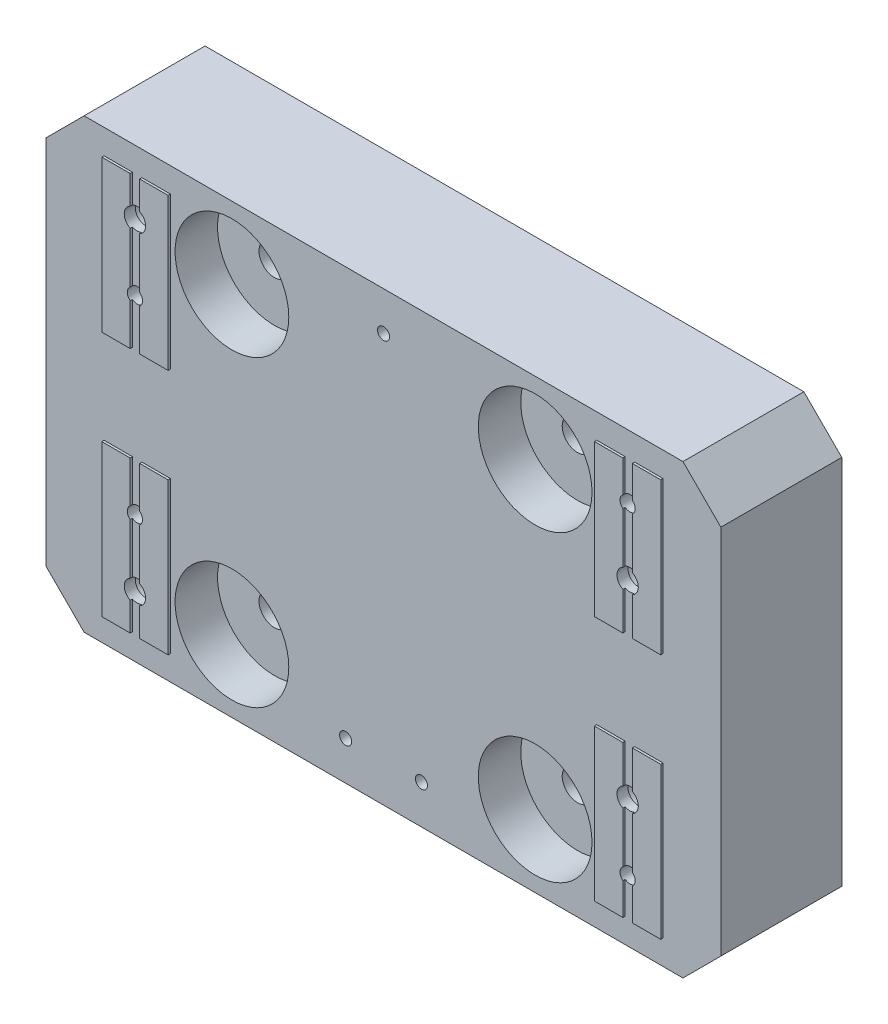
SolidWorks part; units mm, degrees
material "304 SSTL"
ref_plane "Front" through (0, 0, 0) normal (0, 0, 1) x (1, 0, 0)
ref_plane "Top" through (0, 0, 0) normal (0, 1, 0) x (1, 0, 0)
ref_plane "Right" through (0, 0, 0) normal (1, 0, 0) x (0, 0, -1)
sketch "Sketch3" plane through (0, 0, 0) normal (0, 0, 1) x (1, 0, 0)
  line L1 (0, 0) -> (226.06, 0)
  line L2 (0, 0) -> (0, -149.86)
  line L3 (0, -149.86) -> (226.06, -149.86)
  line L4 (226.06, 0) -> (226.06, -149.86)
  dimension "D1" = 226.06
  dimension "D2" = 149.86
extrude "Extrude2" add sketch "Sketch3" along normal blind 41.275
sketch "Sketch4" plane through (0, 0, 41.275) normal (0, 0, 1) x (1, 0, 0)
  line L0 (113.03, 0) -> (113.03, -149.86) construction
  line L1 (0, -74.93) -> (226.06, -74.93) construction
  line L2 (19.3802, -59.055) -> (19.3802, -8.255)
  line L3 (19.3802, -8.255) -> (41.6052, -8.255)
  line L4 (206.6798, -59.055) -> (206.6798, -8.255)
  line L5 (184.4548, -8.255) -> (206.6798, -8.255)
  line L6 (19.3802, -90.805) -> (19.3802, -141.605)
  line L7 (41.6052, -8.255) -> (41.6052, -59.055)
  line L8 (19.3802, -141.605) -> (41.6052, -141.605)
  line L9 (184.4548, -141.605) -> (206.6798, -141.605)
  line L10 (41.6052, -141.605) -> (41.6052, -90.805)
  line L11 (206.6798, -90.805) -> (206.6798, -141.605)
  line L13 (184.4548, -141.605) -> (184.4548, -90.805)
  line L16 (184.4548, -8.255) -> (184.4548, -59.055)
  line L19 (0, 0) -> (226.06, 0)
  line L20 (0, 0) -> (0, -149.86)
  line L21 (0, -149.86) -> (226.06, -149.86)
  line L22 (226.06, 0) -> (226.06, -149.86)
  line L23 (19.3802, -59.055) -> (41.6052, -59.055)
  line L24 (19.3802, -90.805) -> (41.6052, -90.805)
  line L27 (184.4548, -59.055) -> (206.6798, -59.055)
  line L28 (184.4548, -90.805) -> (206.6798, -90.805)
  dimension "D1" = 71.4248
  dimension "D2" = 71.4248
  dimension "D3" = 22.225
  dimension "D5" = 15.875
  dimension "D6" = 15.875
  dimension "D8" = 50.8
extrude "Extrude4" cut sketch "Sketch4" against normal blind 0.762
hole_wizard "CBORE for 1/4 Socket Head Cap Screw1" positions "3DSketch4" profile "Sketch9" counterbore size "1/4" standard "Ansi Inch" end condition through all
sketch3d "3DSketch4"
  line L1 (226.06, -74.93, 0) -> (0, -74.93, 0) construction
  line L2 (226.06, -149.86, 0) -> (226.06, 0, 0) construction
  line L3 (0, 0, 0) -> (0, -149.86, 0) construction
  line L5 (113.03, 0, 0) -> (113.03, -149.86, 0) construction
  line L6 (226.06, 0, 0) -> (0, 0, 0) construction
  line L7 (0, -149.86, 0) -> (226.06, -149.86, 0) construction
  line L10 (195.58, -43.18, 0) -> (195.58, -74.93, 0) construction
  line L12 (195.58, -74.93, 0) -> (195.58, -106.68, 0) construction
  line L14 (30.48, -20.955, 0) -> (30.48, -74.93, 0) construction
  line L16 (30.48, -74.93, 0) -> (30.48, -128.905, 0) construction
  point P4 (195.58, -106.68, 0)
  point P6 (30.48, -20.955, 0)
  point P8 (30.48, -128.905, 0)
  point P10 (195.58, -43.18, 0)
  dimension "D1" = 82.55
  dimension "D2" = 63.5
  dimension "D3" = 107.95
  dimension "D4" = 82.55
sketch "Sketch9" plane through (195.58, -106.68, 0) normal (1, 0, 0) x (0, 1, 0)
  line L0 (0, 0) -> (0, 41.275)
  line L1 (0, 41.275) -> (3.5712, 41.275)
  line L3 (3.5712, 41.275) -> (3.5712, 37.592)
  line L4 (5.5562, 37.592) -> (3.5712, 37.592)
  line L5 (5.5562, 37.592) -> (5.5562, 0.635)
  line L6 (5.5562, 0.635) -> (6.1913, 0)
  line L7 (6.1913, 0) -> (0, 0)
  line L8 (-5.5562, 0.635) -> (-6.1913, 0) construction
  line L11 (0, -6.35) -> (0, 107.95) construction
  dimension "Thru Hole Dia." = 7.1425
  dimension "Thru Hole Depth" = 41.275
  dimension "C'Bore Dia." = 11.1125
  dimension "C'Bore Depth" = 37.592
  dimension "Near C'Sink Dia." = 12.3825
  dimension "Near C'Sink Angle" = 90
hole_wizard "1/4-20 Tapped Hole1" positions "Sketch13" profile "Sketch12" tap size "1/4-20" standard "Ansi Inch" end condition through all
sketch "Sketch13" plane through (0, 0, 0) normal (0, 0, -1) x (-1, 0, 0)
  line L0 (-226.06, -74.93) -> (0, -74.93) construction
  line L1 (-226.06, -149.86) -> (-226.06, 0) construction
  line L2 (0, 0) -> (0, -149.86) construction
  line L4 (-113.03, 0) -> (-113.03, -149.86) construction
  line L5 (-226.06, 0) -> (0, 0) construction
  line L6 (0, -149.86) -> (-226.06, -149.86) construction
  line L11 (-195.58, -20.955) -> (-195.58, -74.93) construction
  line L13 (-195.58, -74.93) -> (-195.58, -128.905) construction
  line L15 (-30.48, -43.18) -> (-30.48, -74.93) construction
  line L17 (-30.48, -74.93) -> (-30.48, -106.68) construction
  point P3 (-195.58, -20.955)
  point P5 (-195.58, -128.905)
  point P7 (-30.48, -43.18)
  point P9 (-30.48, -106.68)
  dimension "D1" = 82.55
  dimension "D2" = 82.55
  dimension "D3" = 107.95
  dimension "D4" = 63.5
cosmetic thread "Hole Thread5" parameters "D1"=19.05, "D2"=6.35
cosmetic thread "Hole Thread6" parameters "D1"=19.05, "D2"=6.35
cosmetic thread "Hole Thread7" parameters "D1"=19.05, "D2"=6.35
cosmetic thread "Hole Thread8" parameters "D1"=19.05, "D2"=6.35
sketch "Sketch12" plane through (195.58, -20.955, 0) normal (1, 0, 0) x (0, 1, 0)
  line L0 (0, 0) -> (0, 41.275)
  line L1 (0, 41.275) -> (2.5527, 41.275)
  line L2 (2.5527, 41.275) -> (2.5527, 0)
  line L5 (2.5527, 0) -> (0, 0)
  line L11 (0, -6.35) -> (0, 107.95) construction
  dimension "Thru Tap Drill Dia." = 5.1054
  dimension "Thru Tap Drill Depth" = 41.275
hole_wizard "CBORE for 3/8 Socket Head Cap Screw1" positions "Sketch17" profile "Sketch16" counterbore size "3/8" standard "Ansi Inch" end condition through all
sketch "Sketch17" plane through (0, 0, 40.513) normal (0, 0, 1) x (1, 0, 0)
  line L0 (163.83, -125.73) -> (62.23, -125.73) construction
  line L1 (163.83, -125.73) -> (163.83, -24.13) construction
  line L2 (163.83, -24.13) -> (62.23, -24.13) construction
  line L3 (62.23, -125.73) -> (62.23, -24.13) construction
  line L4 (113.03, -149.86) -> (113.03, -125.73) construction
  line L5 (0, -149.86) -> (226.06, -149.86) construction
  line L6 (226.06, -74.93) -> (163.83, -74.93) construction
  line L7 (226.06, -149.86) -> (226.06, 0) construction
  point P0 (163.83, -125.73)
  point P1 (62.23, -125.73)
  point P3 (163.83, -24.13)
  point P5 (62.23, -24.13)
  dimension "D1" = 101.6
  dimension "D2" = 101.6
sketch "Sketch16" plane through (163.83, -125.73, 40.513) normal (1, 0, 0) x (0, -1, 0)
  line L0 (0, 0) -> (0, 40.513)
  line L1 (0, 40.513) -> (5.1587, 40.513)
  line L3 (5.1587, 40.513) -> (5.1587, 14.224)
  line L4 (5.1587, 14.224) -> (19.05, 14.224)
  line L5 (19.05, 14.224) -> (19.05, 0)
  line L7 (19.05, 0) -> (0, 0)
  line L11 (0, -6.35) -> (0, 107.95) construction
  dimension "Thru Hole Dia." = 10.3175
  dimension "Thru Hole Depth" = 40.513
  dimension "C'Bore Dia." = 38.1
  dimension "C'Bore Depth" = 14.224
sketch "Sketch18" plane through (0, 0, 41.275) normal (0, 0, 1) x (1, 0, 0)
  line L0 (30.48, -20.955) -> (30.48, -8.255) construction
  line L1 (28.8925, -8.255) -> (32.0675, -8.255)
  line L2 (28.8925, -8.255) -> (28.8925, -141.605)
  line L3 (28.8925, -141.605) -> (32.0675, -141.605)
  line L4 (32.0675, -8.255) -> (32.0675, -141.605)
  line L5 (193.9925, -8.255) -> (197.1675, -8.255)
  line L6 (193.9925, -8.255) -> (193.9925, -141.605)
  line L7 (193.9925, -141.605) -> (197.1675, -141.605)
  line L8 (197.1675, -8.255) -> (197.1675, -141.605)
  line L9 (195.58, -20.955) -> (195.58, -8.255) construction
  line L10 (41.6052, -8.255) -> (19.3802, -8.255) construction
  line L11 (206.6798, -8.255) -> (184.4548, -8.255) construction
  line L12 (184.4548, -141.605) -> (206.6798, -141.605) construction
  line L13 (19.3802, -141.605) -> (41.6052, -141.605) construction
  dimension "D1" = 3.175
  dimension "D2" = 3.175
extrude "Cut-Extrude1" cut sketch "Sketch18" against normal up to surface (0.762 mm away) up to face at (182.88, -125.73, 40.513)
sketch "Sketch19" plane through (0, 0, 0) normal (0, 0, -1) x (-1, 0, 0)
  line L2 (-113.03, -13.0048) -> (-113.03, 0) construction
  line L3 (-226.06, 0) -> (0, 0) construction
  line L4 (-113.03, -74.93) -> (-113.03, -136.8552) construction
  line L5 (-113.03, -136.8552) -> (-113.03, -149.86) construction
  line L6 (0, -149.86) -> (-226.06, -149.86) construction
  line L16 (-113.03, -13.0048) -> (-113.03, -74.93) construction
  line L17 (-125.73, -136.8552) -> (-100.33, -136.8552) construction
  point P0 (-125.73, -136.8552)
  point P1 (-113.03, -13.0048)
  point P54 (-100.33, -136.8552)
  dimension "D1" = 61.9252
  dimension "D2" = 25.4
  dimension "D4" = 61.9252
hole_wizard "#10-32 Tapped Hole1" positions "Sketch21" profile "Sketch20" tap size "#10-32" standard "Ansi Inch" end condition through all
sketch "Sketch21" plane through (0, 0, 0) normal (0, 0, -1) x (-1, 0, 0)
  point P0 (-113.03, -13.0048)
  point P1 (-100.33, -136.8552)
  point P4 (-125.73, -136.8552)
sketch "Sketch20" plane through (113.03, -13.0048, 0) normal (1, 0, 0) x (0, 1, 0)
  line L0 (0, 0) -> (0, 41.275)
  line L1 (0, 41.275) -> (2.0193, 41.275)
  line L2 (2.0193, 41.275) -> (2.0193, 0)
  line L5 (2.0193, 0) -> (0, 0)
  line L11 (0, -6.35) -> (0, 107.95) construction
  dimension "Thru Tap Drill Dia." = 4.0386
  dimension "Thru Tap Drill Depth" = 41.275
cosmetic thread "Hole Thread9" parameters "D1"=12.7, "D2"=4.826
cosmetic thread "Hole Thread10" parameters "D1"=12.7, "D2"=4.826
cosmetic thread "Hole Thread11" parameters "D1"=12.7, "D2"=4.826
chamfer "Chamfer1" distance 12.7 angle 45 4 edges at (0, -149.86, 20.2565) (0, 0, 20.2565) (226.06, -149.86, 20.2565) (226.06, 0, 20.2565)
